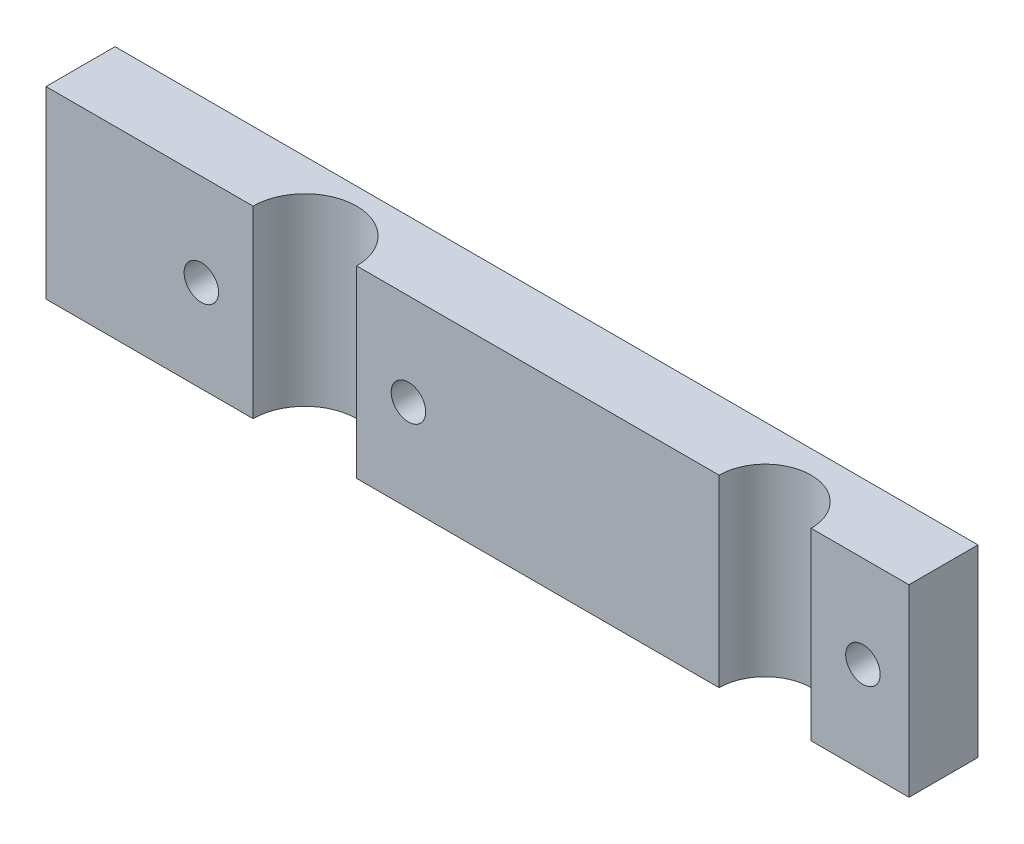
SolidWorks part; units mm, degrees
ref_plane "Ön Düzlem" through (0, 0, 0) normal (0, 0, 1) x (1, 0, 0)
ref_plane "Üst Düzlem" through (0, 0, 0) normal (0, 1, 0) x (1, 0, 0)
ref_plane "Sağ Düzlem" through (0, 0, 0) normal (1, 0, 0) x (0, 0, -1)
sketch "Çizim1" plane through (0, 0, 0) normal (0, 0, 1) x (1, 0, 0)
  line L0 (-75, 16) -> (75, -16) construction
  line L1 (-75, 16) -> (75, 16)
  line L2 (-75, 16) -> (-75, -16)
  line L3 (-75, -16) -> (75, -16)
  line L4 (75, 16) -> (75, -16)
  dimension "D1" = 150
  dimension "D2" = 32
extrude "Yükseklik-Ekstrüzyon1" add sketch "Çizim1" along normal blind 12
sketch "Çizim2" plane through (0, 16, 0) normal (0, 1, 0) x (1, 0, 0)
  line L0 (75, -12) -> (-75, -12) construction
  line L1 (75, -12) -> (75, 0) construction
  circle A0 centre (50, -12) radius 8
  circle A1 centre (-30, -12) radius 9
  dimension "D1" = 80
  dimension "D3" = 18
  dimension "D4" = 16
  dimension "D2" = 25
extrude "Kes-Ekstrüzyon1" cut sketch "Çizim2" against normal blind 60
sketch "Çizim3" plane through (0, 0, 12) normal (0, 0, 1) x (1, 0, 0)
  line L0 (75, -16) -> (75, 16) construction
  line L1 (75, 0) -> (59.3975, 0) construction
  line L2 (-21, 16) -> (-39, 16) construction
  circle A0 centre (67, 0) radius 3
  circle A1 centre (-48, 0) radius 3
  circle A2 centre (-12, 0) radius 3
  point P2 (75, 0)
  point P12 (-30, 16)
  dimension "D1" = 8
  dimension "D2" = 36
  dimension "D3" = 18
extrude "Kes-Ekstrüzyon2" cut sketch "Çizim3" against normal blind 30
